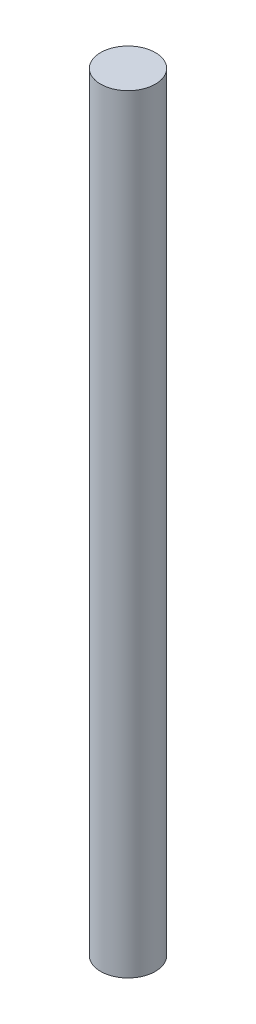
SolidWorks part; units mm, degrees
ref_plane "Front Plane" through (0, 0, 0) normal (0, 0, 1) x (1, 0, 0)
ref_plane "Top Plane" through (0, 0, 0) normal (0, 1, 0) x (1, 0, 0)
ref_plane "Right Plane" through (0, 0, 0) normal (1, 0, 0) x (0, 0, -1)
sketch "Sketch1" plane through (0, 0, 0) normal (0, 1, 0) x (1, 0, 0)
  circle A0 centre (0, 0) radius 2.5
  dimension "D1" = 5
extrude "Boss-Extrude1" add sketch "Sketch1" along normal blind 20.2 and the other way blind 50
